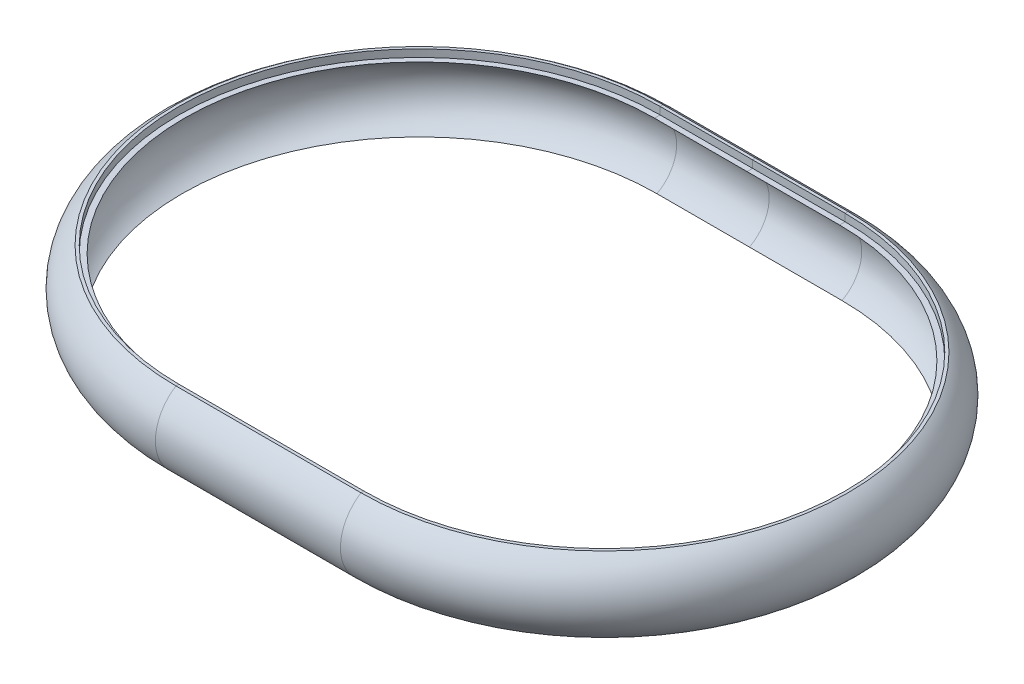
SolidWorks part; units mm, degrees
ref_plane "Front Plane" through (0, 0, 0) normal (0, 0, 1) x (1, 0, 0)
ref_plane "Top Plane" through (0, 0, 0) normal (0, 1, 0) x (1, 0, 0)
ref_plane "Right Plane" through (0, 0, 0) normal (1, 0, 0) x (0, 0, -1)
sketch "Sketch1" plane through (0, 0, 0) normal (1, 0, 0) x (0, 0, -1)
  line L0 (130.8, 8.0398) -> (130, 8.0398)
  line L1 (130, 8.0398) -> (130, 6.0398)
  line L2 (130, 6.0398) -> (128.5, 6.0398)
  line L4 (129.1501, -11.9602) -> (131.1501, -11.9602)
  arc A0 (128.5, 6.0398) -> (129.1501, -11.9602) centre (124.4811, -3.1171) cw
  arc A1 (130.8, 8.0398) -> (131.1501, -11.9602) centre (124.3451, -2.0763) cw
  point P4 (8.7963, -5.6665)
  point P9 (9.4741, 1.9589)
  point P10 (10.9653, 2.84)
  point P11 (0, 0)
  point P12 (12.1854, -5.497)
  point P13 (0, 0)
  point P14 (0, 0)
  dimension "D6" = 2
  dimension "D7" = 12
  dimension "D8" = 10
  dimension "D1" = 0.8
  dimension "D2" = 2
  dimension "D3" = 1.5
  dimension "D4" = 18
  dimension "D9" = 130
ref_plane "Plane1" through (0, 6.0398, 0) normal (0, 1, 0) x (1, 0, 0)
sketch "Sketch3" plane through (0, 6.0398, 0) normal (0, 1, 0) x (1, 0, 0)
  line L0 (-25, 130) -> (25, 130)
  line L1 (-25, 0) -> (25, 0)
  arc A0 (-25, 130) -> (-25, 0) centre (-25, 65) ccw
  arc A1 (25, 130) -> (25, 0) centre (25, 65) cw
  dimension "D3" = 65
  dimension "D1" = 50
  dimension "D2" = 50
sweep "Sweep1" add profiles "Sketch1" path "Sketch3"
